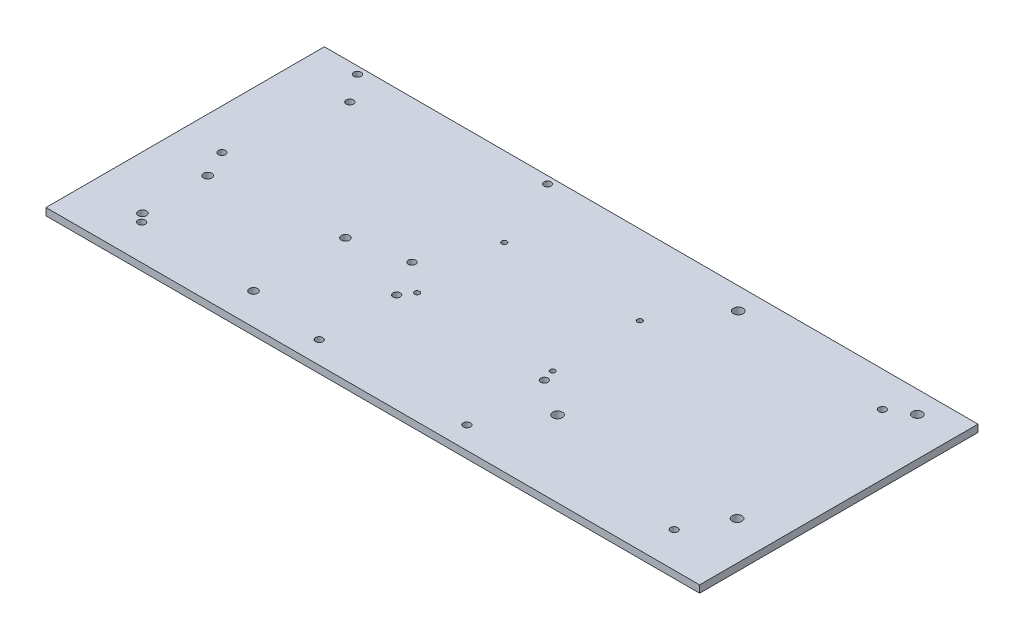
SolidWorks part; units mm, degrees
ref_plane "Alzado" through (0, 0, 0) normal (0, 0, 1) x (1, 0, 0)
ref_plane "Planta" through (0, 0, 0) normal (0, 1, 0) x (1, 0, 0)
ref_plane "Vista lateral" through (0, 0, 0) normal (1, 0, 0) x (0, 0, -1)
sketch "Croquis1" plane through (0, 0, 0) normal (0, 1, 0) x (1, 0, 0)
  line L1 (-125, 60) -> (125, 60)
  line L2 (-125, 60) -> (-125, -55)
  line L3 (-125, -55) -> (125, -55)
  line L4 (125, 60) -> (125, -55)
  dimension "D1" = 250
  dimension "D2" = 115
  dimension "D3" = 125
  dimension "D4" = 60
extrude "Saliente-Extruir1" add sketch "Croquis1" along normal blind 3
sketch "Croquis3" plane through (0, 3, 0) normal (0, 1, 0) x (1, 0, 0)
  line L0 (-118.3314, 57) -> (-39.8314, 57) construction
  line L1 (-39.8314, 57) -> (-39.8314, 1) construction
  line L2 (-27.8496, 27.1538) -> (28.1504, 27.1538) construction
  line L3 (-62.3, -4) -> (-62.3, -42) construction
  line L4 (-113, -10.2) -> (-113, -37.16) construction
  line L5 (-125, 60) -> (-125, -55) construction
  line L6 (-125, 0) -> (125, 0) construction
  line L7 (0, 55) -> (0, -55) construction
  line L8 (-31.3, -13.8462) -> (-31.3, -45.8462) construction
  line L9 (-31.3, -45.8462) -> (29.7, -45.8462) construction
  line L10 (29.7, -45.8462) -> (29.7, -13.8462) construction
  line L11 (29.7, -13.8462) -> (-31.3, -13.8462) construction
  line L12 (-39.8314, 1) -> (-118.3314, 1) construction
  line L13 (-118.3314, 1) -> (-118.3314, 57) construction
  line L14 (28.1504, 27.1538) -> (28.1504, -8.8462) construction
  line L15 (28.1504, -8.8462) -> (-27.8496, -8.8462) construction
  line L16 (-27.8496, -8.8462) -> (-27.8496, 27.1538) construction
  line L17 (45, 50.9662) -> (119, 50.9662) construction
  line L18 (125, -55) -> (125, 60) construction
  line L19 (119, 50.9662) -> (119, -23.5338) construction
  line L20 (119, -23.5338) -> (45, -23.5338) construction
  line L21 (45, -23.5338) -> (45, 50.9662) construction
  line L22 (-125, -55) -> (125, -55) construction
  circle A0 centre (-39.8314, 1) radius 1.5
  circle A1 centre (-118.3314, 1) radius 1.5
  circle A2 centre (-118.3314, 57) radius 1.5
  circle A3 centre (-39.8314, 57) radius 1.5
  circle A5 centre (45, 50.9662) radius 2
  circle A6 centre (119, 50.9662) radius 2
  circle A7 centre (44.8512, -23.5338) radius 2
  circle A8 centre (119, -23.5338) radius 2
  circle A12 centre (-31.3, -13.8462) radius 1.5
  circle A13 centre (-31.3, -45.8462) radius 1.5
  circle A14 centre (29.7, -45.8462) radius 1.5
  circle A15 centre (29.7, -13.8462) radius 1.5
  circle A16 centre (-27.8496, 27.1538) radius 1.05
  circle A17 centre (-27.8496, -8.8462) radius 1.05
  circle A18 centre (28.1504, -8.8462) radius 1.05
  circle A19 centre (28.1504, 27.1538) radius 1.05
  circle A20 centre (-113, -10.2) radius 1.7
  circle A21 centre (-113, -37.16) radius 1.7
  circle A22 centre (-62.3, -4) radius 1.7
  circle A23 centre (-62.3, -42) radius 1.7
  point P20 (0, 0)
  point P23 (0, 0)
  point P51 (0, 0)
  point P58 (0, 0)
  dimension "D12" = 3
  dimension "D9" = 2.1
  dimension "D19" = 4
  dimension "D3" = 3.4
  dimension "D2" = 56
  dimension "D4" = 50.7
  dimension "D5" = 78.5
  dimension "D6" = 5
  dimension "D7" = 56
  dimension "D8" = 36
  dimension "D10" = 26.96
  dimension "D11" = 6.2
  dimension "D13" = 38
  dimension "D14" = 32
  dimension "D15" = 61
  dimension "D16" = 61
  dimension "D18" = 32
  dimension "D20" = 6
  dimension "D21" = 74
  dimension "D22" = 74.5
  dimension "D23" = 74
  dimension "D24" = 74.5
  dimension "D25" = 5
  dimension "D26" = 12
  dimension "D27" = 39.8314
  dimension "D28" = 45
  dimension "D29" = 13.8462
  dimension "D30" = 15.3
  dimension "D31" = 31
  dimension "D32" = 11.9818
  dimension "D33" = 6.6686
  dimension "D34" = 16.7008
  dimension "D35" = 90.8496
  dimension "D36" = 89.3
  dimension "D37" = 90.8496
extrude "Cortar-Extruir1" cut sketch "Croquis3" against normal blind 10
sketch "Croquis4" plane through (-125, 0, 0) normal (-1, 0, 0) x (0, 0, 1)
  line L1 (-60, 3) -> (55, 3)
  line L2 (-60, 3) -> (-60, 0)
  line L3 (-60, 0) -> (55, 0)
  line L4 (55, 3) -> (55, 0)
extrude "Saliente-Extruir2" add sketch "Croquis4" along normal blind 10
sketch "Croquis5" plane through (125, 0, 0) normal (1, 0, 0) x (0, 0, -1)
  line L1 (-55, 3) -> (60, 3)
  line L2 (-55, 3) -> (-55, 0)
  line L3 (-55, 0) -> (60, 0)
  line L4 (60, 3) -> (60, 0)
extrude "Saliente-Extruir3" add sketch "Croquis5" along normal blind 10
sketch "Croquis6" plane through (0, 3, 0) normal (0, 1, 0) x (1, 0, 0)
  line L0 (-135, -55) -> (-135, 60) construction
  line L1 (135, 60) -> (-135, 60) construction
  line L2 (-135, -55) -> (135, -55) construction
  line L3 (135, 60) -> (135, -55) construction
  circle A0 centre (-110, 45.4952) radius 1.5
  circle A1 centre (-110, -40.5) radius 1.5
  circle A2 centre (110, 45.4952) radius 1.5
  circle A3 centre (110, -40.5) radius 1.5
  point P14 (-125.4626, -32.0476)
  dimension "D1" = 3
  dimension "D2" = 25
  dimension "D3" = 14.5048
  dimension "D4" = 25
  dimension "D5" = 25
  dimension "D6" = 14.5
  dimension "D7" = 25
  dimension "D8" = 14.5
  dimension "D9" = 14.5048
extrude "Cortar-Extruir2" cut sketch "Croquis6" against normal blind 50
